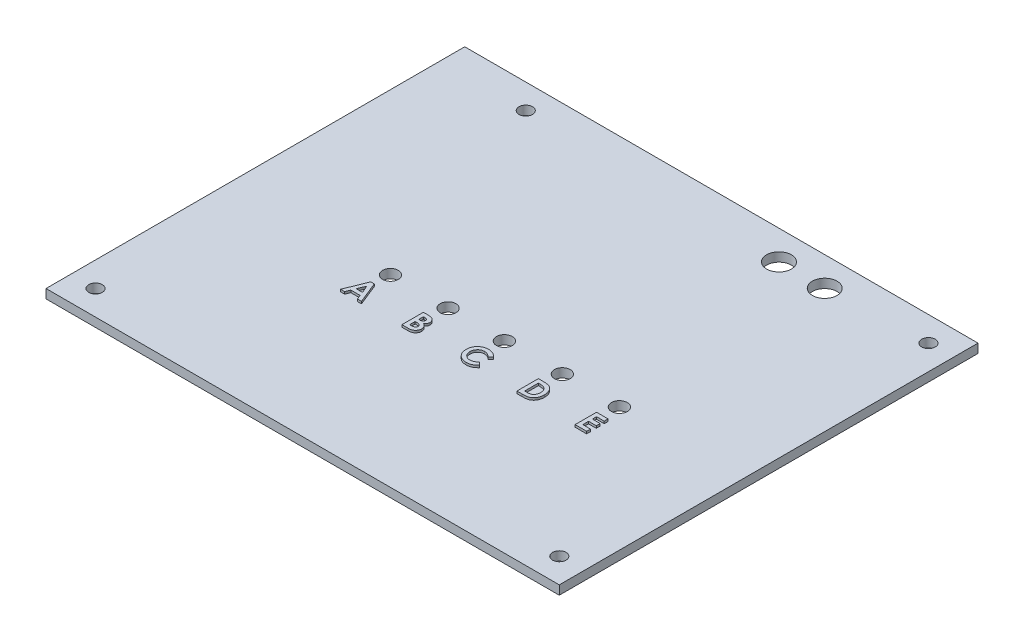
SolidWorks part; units mm, degrees
ref_plane "Front" through (0, 0, 0) normal (0, 0, 1) x (1, 0, 0)
ref_plane "Top" through (0, 0, 0) normal (0, 1, 0) x (1, 0, 0)
ref_plane "Right" through (0, 0, 0) normal (1, 0, 0) x (0, 0, -1)
sketch "Sketch1" plane through (0, 0, 0) normal (0, 1, 0) x (1, 0, 0)
  line L1 (-49.4444, 29) -> (64.5556, 29)
  line L2 (-49.4444, 29) -> (-49.4444, -64)
  line L3 (-49.4444, -64) -> (64.5556, -64)
  line L4 (64.5556, 29) -> (64.5556, -64)
  dimension "D1" = 114
  dimension "D2" = 93
extrude "Boss-Extrude1" add sketch "Sketch1" along normal blind 2
sketch "Sketch2" plane through (0, 2, 0) normal (0, 1, 0) x (1, 0, 0)
  circle A0 centre (-30.3858, 23.5) radius 1.5
  circle A1 centre (59.0556, 23.5) radius 1.5
  circle A2 centre (59.0556, -58.5) radius 1.5
  circle A3 centre (-43.9444, -58.5) radius 1.5
extrude "Cut-Extrude1" cut sketch "Sketch2" against normal up to next
sketch "Sketch3" plane through (0, 2, 0) normal (0, 1, 0) x (1, 0, 0)
  circle A0 centre (-13.811, -23.1251) radius 1.75
  circle A1 centre (-1.0065, -23.1347) radius 1.75
  circle A2 centre (11.5606, -23.2041) radius 1.75
  circle A3 centre (24.3544, -23.1211) radius 1.75
  circle A4 centre (37.0276, -23.1274) radius 1.75
  circle A5 centre (26.8357, 22.52) radius 2.75
  circle A6 centre (36.9957, 22.52) radius 2.75
  dimension "D1" = 3.5
  dimension "D2" = 3.5
  dimension "D3" = 3.5
  dimension "D4" = 3.5
  dimension "D5" = 3.5
  dimension "D6" = 5.5
  dimension "D7" = 5.5
extrude "Cut-Extrude2" cut sketch "Sketch3" against normal up to next
sketch "Sketch4" plane through (0, 2, 0) normal (0, 1, 0) x (1, 0, 0)
  text T0 "<b>A B C D E</b>" font "Century Gothic" height in points 18
extrude "Boss-Extrude2" add sketch "Sketch4" along normal blind 0.5
